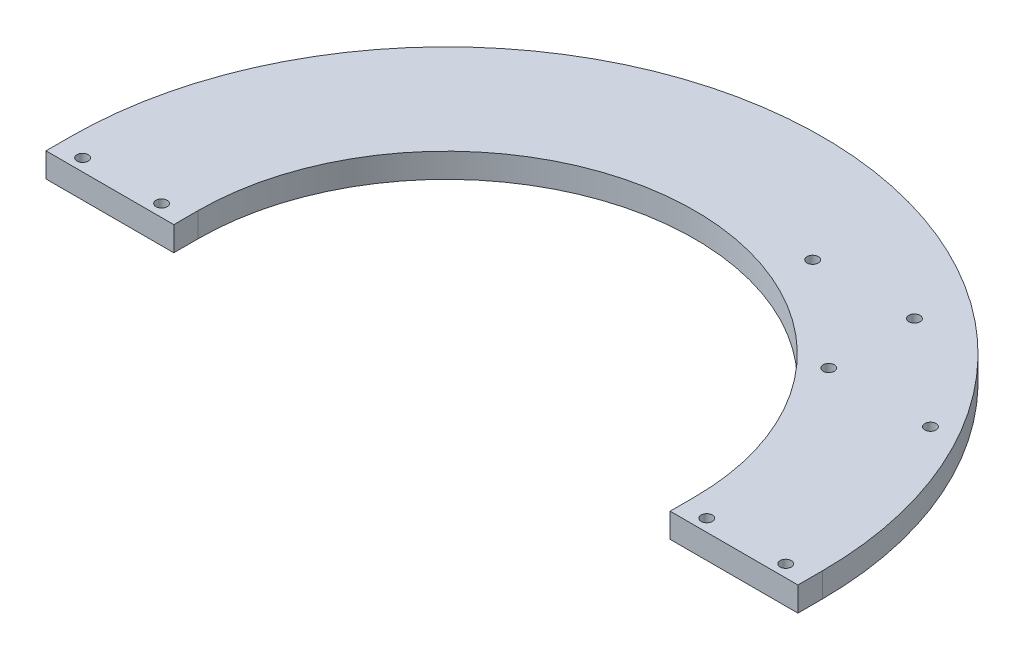
SolidWorks part; units mm, degrees
ref_plane "Front Plane" through (0, 0, 0) normal (0, 0, 1) x (1, 0, 0)
ref_plane "Top Plane" through (0, 0, 0) normal (0, 1, 0) x (1, 0, 0)
ref_plane "Right Plane" through (0, 0, 0) normal (1, 0, 0) x (0, 0, -1)
sketch "Sketch1" plane through (0, 0, 0) normal (0, 1, 0) x (1, 0, 0)
  line L2 (-117.3163, 0) -> (-117.3163, -7.62)
  line L3 (-117.3163, -7.62) -> (-77.4382, -7.62)
  line L4 (-77.4382, -7.62) -> (-77.4382, 0)
  line L5 (77.4382, 0) -> (77.4382, -7.62)
  line L6 (77.4382, -7.62) -> (117.3163, -7.62)
  line L7 (117.3163, -7.62) -> (117.3163, 0)
  arc A0 (77.4382, 0) -> (-77.4382, 0) centre (0, 0) ccw
  arc A1 (117.3163, 0) -> (-117.3163, 0) centre (0, 0) ccw
  dimension "D1" = 39.878
  dimension "D2" = 154.8765
  dimension "D3" = 7.62
  dimension "D4" = 7.62
extrude "Boss-Extrude1" add sketch "Sketch1" along normal blind 7.62
sketch "Sketch3" plane through (0, 7.62, 0) normal (0, 1, 0) x (1, 0, 0)
  line L0 (-117.3163, -7.62) -> (-77.4382, -7.62) construction
  line L1 (-77.4382, -7.62) -> (-77.4382, 0) construction
  line L2 (-117.3163, 0) -> (-117.3163, -7.62) construction
  line L3 (77.4382, -7.62) -> (117.3163, -7.62) construction
  line L4 (77.4382, 0) -> (77.4382, -7.62) construction
  line L5 (117.3163, -7.62) -> (117.3163, 0) construction
  circle A0 centre (-109.6963, -3.81) radius 1.7526
  circle A1 centre (-85.0583, -3.81) radius 1.7526
  circle A2 centre (85.0583, -3.81) radius 1.7526
  circle A3 centre (109.6963, -3.81) radius 1.7526
  circle A5 centre (31.75, 82.55) radius 1.7526
  circle A6 centre (63.5, 82.55) radius 1.7526
  circle A7 centre (63.5, 55.8124) radius 1.7526
  circle A8 centre (95.25, 55.8124) radius 1.7526
  dimension "D1" = 3.5052
  dimension "D2" = 3.5052
  dimension "D3" = 3.5052
  dimension "D4" = 3.5052
  dimension "D5" = 3.81
  dimension "D6" = 7.62
  dimension "D7" = 7.62
  dimension "D8" = 3.81
  dimension "D9" = 3.81
  dimension "D10" = 3.81
  dimension "D11" = 7.62
  dimension "D12" = 7.62
  dimension "D13" = 3.5052
  dimension "D14" = 3.5052
  dimension "D15" = 82.55
  dimension "D16" = 82.55
  dimension "D17" = 31.75
  dimension "D18" = 63.5
  dimension "D19" = 3.5052
  dimension "D20" = 3.5052
  dimension "D21" = 31.75
  dimension "D22" = 63.5
extrude "Cut-Extrude1" cut sketch "Sketch3" against normal up to next
